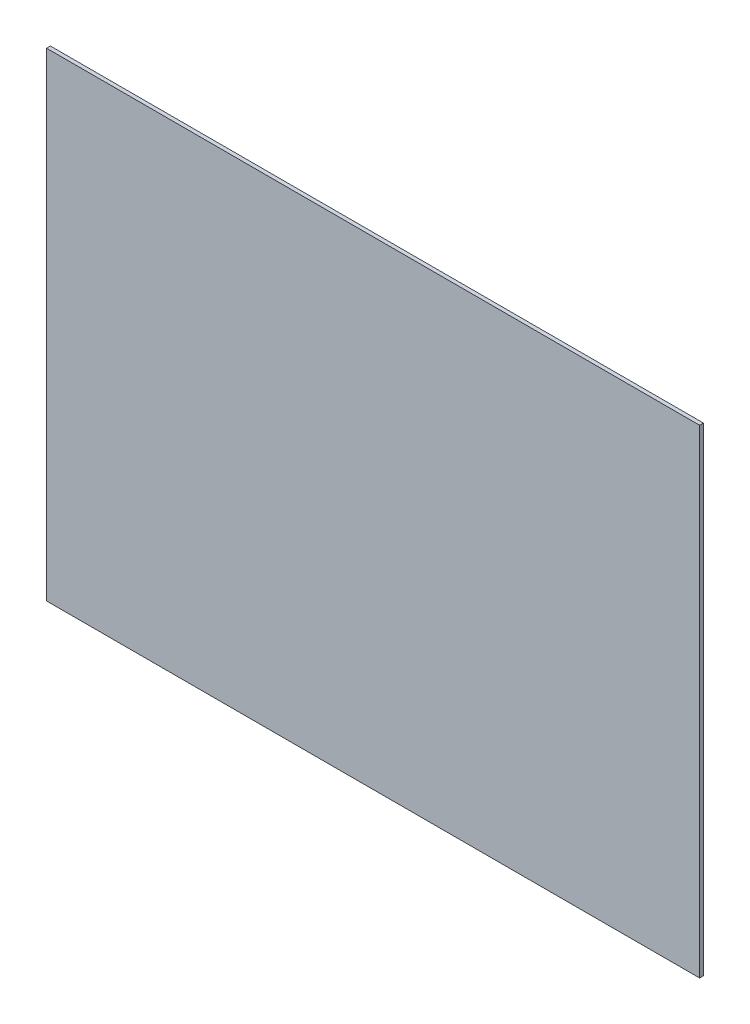
SolidWorks part; units mm, degrees
ref_plane "Front Plane" through (0, 0, 0) normal (0, 0, 1) x (1, 0, 0)
ref_plane "Top Plane" through (0, 0, 0) normal (0, 1, 0) x (1, 0, 0)
ref_plane "Right Plane" through (0, 0, 0) normal (1, 0, 0) x (0, 0, -1)
sketch "Sketch1" plane through (0, 0, 0) normal (0, 0, 1) x (1, 0, 0)
  line L1 (-136.525, 100.076) -> (136.525, 100.076)
  line L2 (-136.525, 100.076) -> (-136.525, -100.076)
  line L3 (-136.525, -100.076) -> (136.525, -100.076)
  line L4 (136.525, 100.076) -> (136.525, -100.076)
  line L5 (-136.525, 100.076) -> (136.525, -100.076) construction
  line L6 (-136.525, -100.076) -> (136.525, 100.076) construction
  point P0 (0, 0)
  dimension "D1" = 273.05
  dimension "D2" = 200.152
extrude "Boss-Extrude1" add sketch "Sketch1" along normal blind 1.6002
